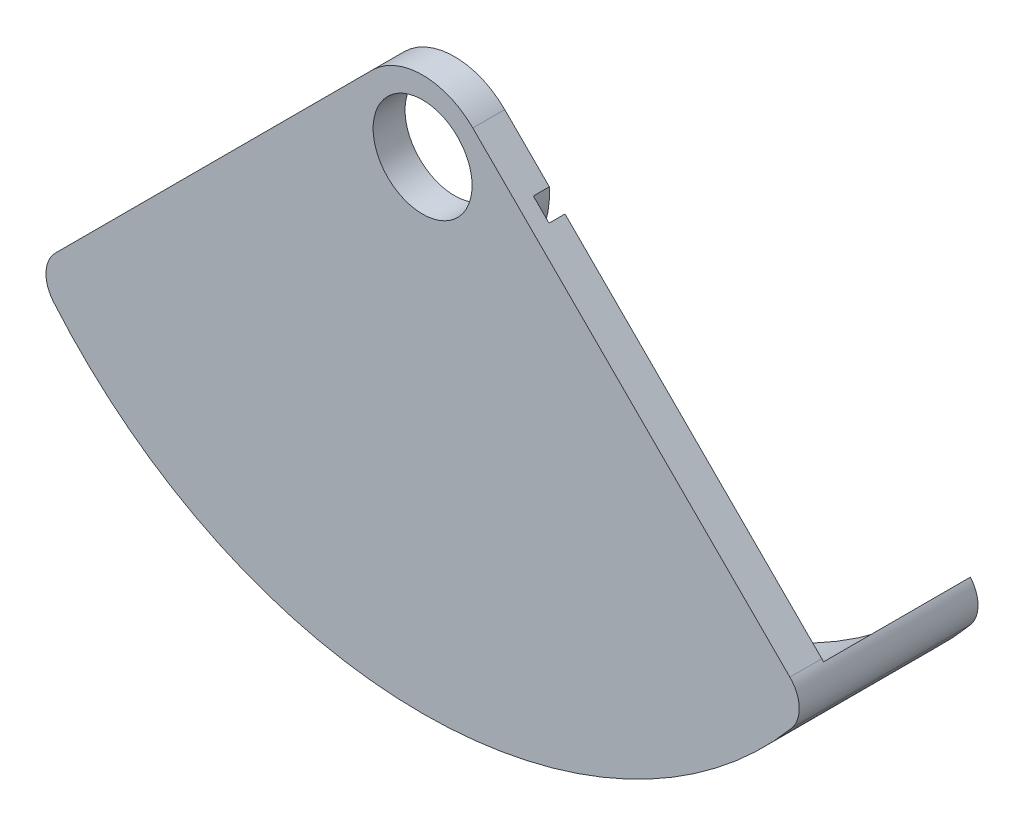
SolidWorks part; units mm, degrees
ref_plane "Alzado" through (0, 0, 0) normal (0, 0, 1) x (1, 0, 0)
ref_plane "Planta" through (0, 0, 0) normal (0, 1, 0) x (1, 0, 0)
ref_plane "Vista lateral" through (0, 0, 0) normal (1, 0, 0) x (0, 0, -1)
sketch "Croquis1" plane through (0, 0, 0) normal (0, 0, 1) x (1, 0, 0)
  line L0 (-1.5733, 1.5733) -> (-11.5058, -8.3592)
  line L1 (1.5733, 1.5733) -> (11.5058, -8.3592)
  line L2 (0, 0) -> (0, -50000) construction
  line L3 (0, 0) -> (-50000, 0) construction
  arc A0 (1.5733, 1.5733) -> (-1.5733, 1.5733) centre (0, 0) ccw
  arc A1 (-11.5646, -9.7093) -> (11.5646, -9.7093) centre (0, 0) ccw
  circle A2 centre (0, 0) radius 14.3 construction
  circle A3 centre (0, 0) radius 15.1 construction
  circle A4 centre (0, 0) radius 1.55
  arc A5 (11.5058, -8.3592) -> (11.5646, -9.7093) centre (10.7987, -9.0663) cw
  arc A6 (-11.5058, -8.3592) -> (-11.5646, -9.7093) centre (-10.7987, -9.0663) ccw
  point P16 (12.1341, -8.9874)
  point P19 (-12.1341, -8.9874)
  dimension "D1" = 4.45
  dimension "D2" = 28.6
  dimension "D4" = 3.1
  dimension "D5" = 1
  dimension "D3" = 0.8
  dimension "D6" = 45
extrude "Saliente-Extruir1" add sketch "Croquis1" against normal blind 1
sketch "Croquis3" plane through (0, 0, -1) normal (0, 0, -1) x (-1, 0, 0)
  line L0 (0, 200000) -> (0, -250000) construction
  line L2 (-1.5733, 1.5733) -> (-11.5058, -8.3592)
  line L3 (11.5058, -8.3592) -> (1.5733, 1.5733)
  line L4 (-2.9697, 0.1769) -> (-3.4608, -0.3141)
  line L5 (3.4608, -0.3141) -> (2.9697, 0.1769)
  circle A0 centre (0, 0) radius 1.55 construction
  circle A1 centre (0, 0) radius 1.55
  arc A2 (-3.4608, -0.3141) -> (3.4608, -0.3141) centre (0, 0) ccw
  arc A3 (-2.9697, 0.1769) -> (2.9697, 0.1769) centre (0, 0) ccw
  arc A4 (1.5733, 1.5733) -> (-1.5733, 1.5733) centre (0, 0) ccw
  arc A5 (-11.5058, -8.3592) -> (-11.5646, -9.7093) centre (-10.7987, -9.0663) ccw
  arc A6 (-11.5646, -9.7093) -> (11.5646, -9.7093) centre (0, 0) ccw
  arc A7 (11.5646, -9.7093) -> (11.5058, -8.3592) centre (10.7987, -9.0663) ccw
  circle A12 centre (0, 0) radius 3.475 construction
  circle A13 centre (0, 0) radius 2.975 construction
  circle A14 centre (0, 0) radius 14.3 construction
  point P21 (0, -14.3)
  point P22 (0, 1.55)
  dimension "D2" = 6.95
  dimension "D1" = 0
  dimension "D3" = 0.5
extrude "Cortar-Extruir1" cut sketch "Croquis3" against normal blind 0.5
sketch "Croquis4" plane through (0, 0, -1) normal (0, 0, -1) x (-1, 0, 0)
  line L2 (11.5058, -8.3592) -> (3.4608, -0.3141)
  line L3 (-3.4608, -0.3141) -> (-11.5058, -8.3592)
  circle A0 centre (0, 0) radius 14.3 construction
  arc A1 (-11.5599, -8.4178) -> (11.5599, -8.4178) centre (0, 0) ccw
  arc A4 (-3.4608, -0.3141) -> (3.4608, -0.3141) centre (0, 0) ccw
  arc A5 (-11.5058, -8.3592) -> (-11.5646, -9.7093) centre (-10.7987, -9.0663) ccw
  arc A6 (-11.5646, -9.7093) -> (11.5646, -9.7093) centre (0, 0) ccw
  arc A7 (11.5646, -9.7093) -> (11.5058, -8.3592) centre (10.7987, -9.0663) ccw
  arc A9 (-11.5599, -8.4178) -> (-11.5646, -9.7093) centre (-10.7987, -9.0663) ccw
  arc A10 (-11.5646, -9.7093) -> (11.5646, -9.7093) centre (0, 0) ccw
  arc A11 (11.5646, -9.7093) -> (11.5599, -8.4178) centre (10.7987, -9.0663) ccw
  dimension "D1" = 0
extrude "Saliente-Extruir2" add sketch "Croquis4" along normal blind 4.6
sketch "Croquis5" plane through (0, 0, -1) normal (0, 0, -1) x (-1, 0, 0)
  line L0 (0, 200000) -> (0, -250000) construction
  circle A0 centre (0, 0) radius 14.3 construction
  arc A1 (-3.4608, -0.3141) -> (3.4608, -0.3141) centre (0, 0) ccw construction
  point P0 (0, 14.3)
  point P1 (0, -3.475)
ref_plane "Plano4" through (0, 0, -3.3) normal (0, 0, -1) x (-1, 0, 0)
sketch "Croquis6" plane through (0, 0, -3.3) normal (0, 0, -1) x (-1, 0, 0)
  circle A0 centre (0, 0) radius 14.3 construction
  arc A1 (-11.5599, -8.4178) -> (11.5599, -8.4178) centre (0, 0) ccw
sketch "Croquis44" plane through (-1.5733, 1.5733, 0) normal (-0.7071, 0.7071, 0) x (0, 0, 1)
  circle A0 centre (-3.3, -14.1263) radius 0.4103
